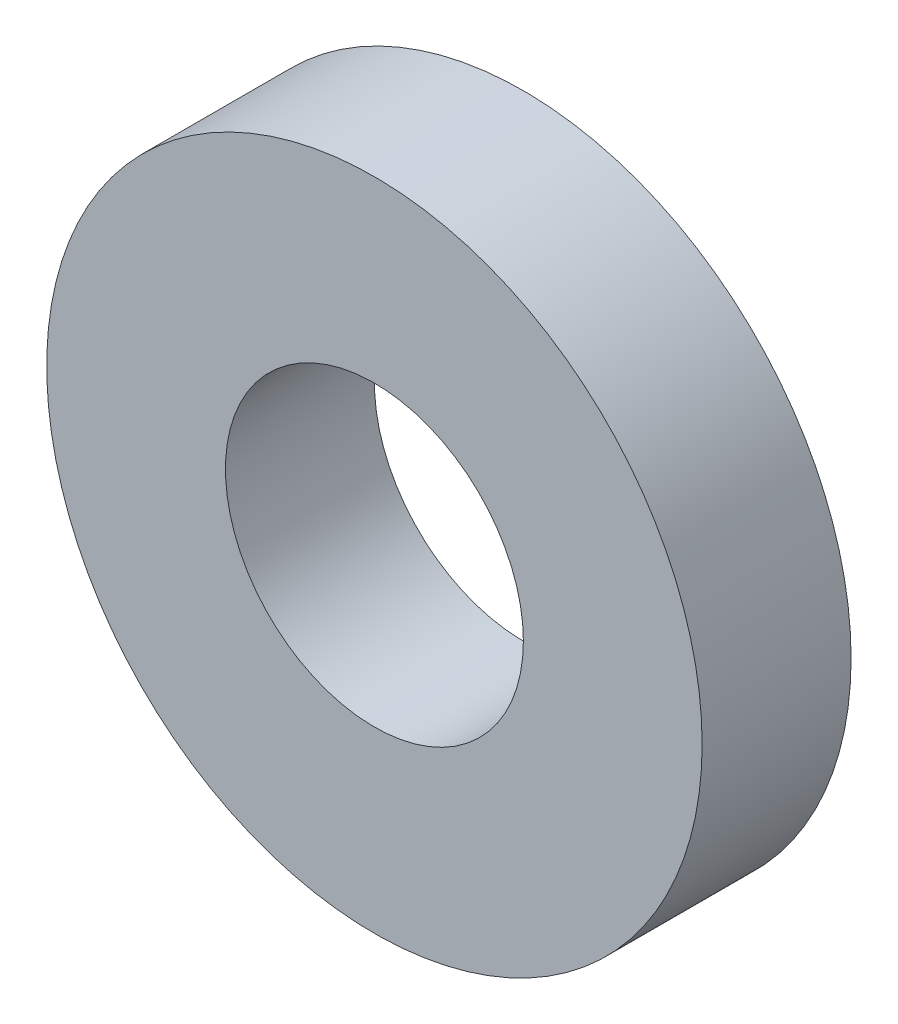
SolidWorks part; units mm, degrees
ref_plane "Front Plane" through (0, 0, 0) normal (0, 0, 1) x (1, 0, 0)
ref_plane "Top Plane" through (0, 0, 0) normal (0, 1, 0) x (1, 0, 0)
ref_plane "Right Plane" through (0, 0, 0) normal (1, 0, 0) x (0, 0, -1)
sketch "Sketch1" plane through (0, 0, 0) normal (0, 0, 1) x (1, 0, 0)
  circle A0 centre (0, 0) radius 6
  circle A1 centre (0, 0) radius 13.2
extrude "Boss-Extrude1" add sketch "Sketch1" along normal blind 6
sketch "Sketch2" plane through (0, 0, 6) normal (0, 0, 1) x (1, 0, 0)
  line L0 (0, 0) -> (0, 15.2) construction
  line L1 (-1.8199, 15.2) -> (0, 0) construction
  line L2 (1.8199, 15.2) -> (0, 0) construction
  arc A0 (-1.8199, 12) -> (1.8199, 12) centre (0, 0) cw
  arc A1 (-3.8199, 12.6352) -> (3.8199, 12.6352) centre (0, 0) cw
  arc A2 (-1.8199, 10.512) -> (1.8199, 10.512) centre (0, 0) cw
  arc A3 (-3.8199, 12.6352) -> (-1.8199, 10.512) centre (-3.157, 11.256) cw
  arc A4 (3.8199, 12.6352) -> (1.8199, 10.512) centre (3.157, 11.256) ccw
